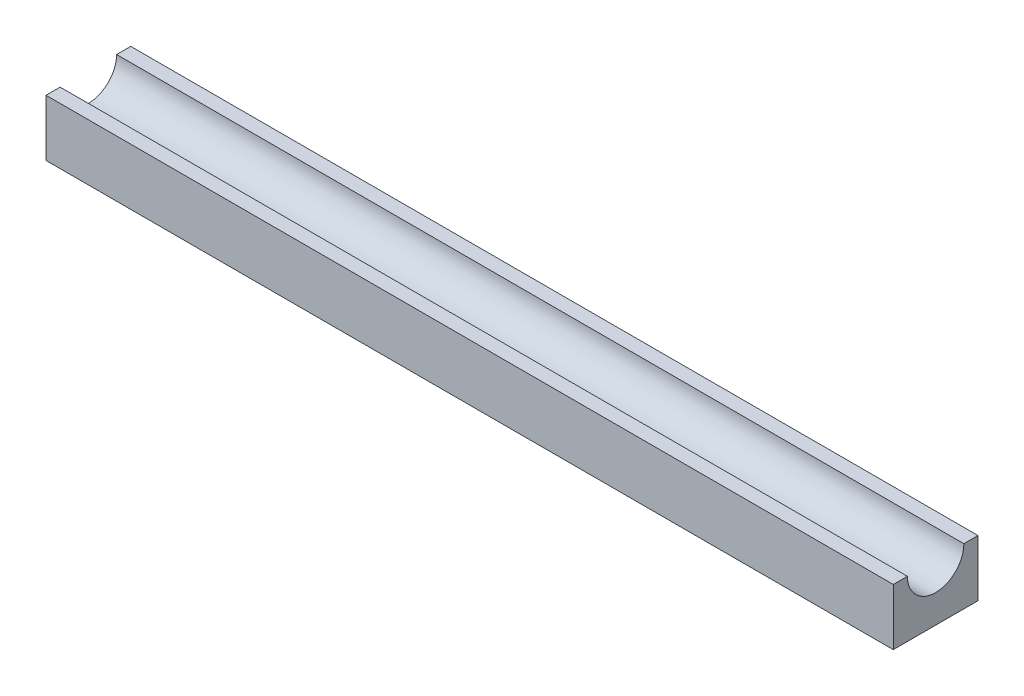
SolidWorks part; units mm, degrees
ref_plane "Front Plane" through (0, 0, 0) normal (0, 0, 1) x (1, 0, 0)
ref_plane "Top Plane" through (0, 0, 0) normal (0, 1, 0) x (1, 0, 0)
ref_plane "Right Plane" through (0, 0, 0) normal (1, 0, 0) x (0, 0, -1)
sketch "Sketch1" plane through (0, 0, 0) normal (1, 0, 0) x (0, 0, -1)
  line L1 (-7.5, 5) -> (7.5, 5)
  line L2 (-7.5, 5) -> (-7.5, -5)
  line L3 (-7.5, -5) -> (7.5, -5)
  line L4 (7.5, 5) -> (7.5, -5)
  line L5 (-7.5, 5) -> (7.5, -5) construction
  line L6 (-7.5, -5) -> (7.5, 5) construction
  circle A1 centre (0, 5) radius 5
  point P0 (0, 0)
  dimension "D3" = 10
  dimension "D1" = 10
  dimension "D2" = 15
extrude "Boss-Extrude1" add sketch "Sketch1" along normal blind 150
ref_plane "Plane1" through (15, 0, 0) normal (-1, 0, 0) x (0, 0, 1)
sketch "Sketch3" plane through (15, 0, 0) normal (-1, 0, 0) x (0, 0, 1)
  line L0 (7.5, -5) -> (-7.5, -5) construction
  line L1 (1.5, -5) -> (-1.5, -5)
  line L2 (1.5, -5) -> (1.5, -7)
  line L3 (1.5, -7) -> (-1.5, -7)
  line L4 (-1.5, -5) -> (-1.5, -7)
  line L5 (1.5, -5) -> (-1.5, -7) construction
  line L6 (1.5, -7) -> (-1.5, -5) construction
  arc A0 (-1.5, -7) -> (1.5, -7) centre (0, -7) ccw
  circle A1 centre (0, -7) radius 0.5
  point P0 (0, -6)
  point P7 (0, -5)
  point P8 (0, -5)
  dimension "D3" = 1
  dimension "D1" = 2
  dimension "D2" = 3
ref_plane "Plane2" through (82.5, 0, 0) normal (1, 0, 0) x (0, 0, -1)
ref_plane "Plane3" through (0, 0, 0) normal (0, 0, 1) x (1, 0, 0)
sketch "Sketch6" plane through (0, 0, 0) normal (0, 0, 1) x (1, 0, 0)
  line L0 (150, -5) -> (0, -5) construction
  line L1 (72.5, -5) -> (77.5, -5)
  line L2 (72.5, -5) -> (72.5, -8)
  line L3 (72.5, -8) -> (77.5, -8)
  line L4 (77.5, -5) -> (77.5, -8)
  line L5 (72.5, -5) -> (77.5, -8) construction
  line L6 (72.5, -8) -> (77.5, -5) construction
  line L7 (150, -5) -> (0, -5)
  line L8 (150, 5) -> (150, -5) construction
  circle A0 centre (75, -8) radius 2.5
  point P0 (75, -6.5)
  dimension "D1" = 5
  dimension "D2" = 75
  dimension "D3" = 3
extrude "Boss-Extrude6" add sketch "Sketch6" along normal mid plane 3 contours L3 A0 | L3 A0 | A0 L4 L1 L2
sketch "Sketch7" plane through (0, 0, 0) normal (0, 0, 1) x (1, 0, 0)
  arc A0 (72.5, -8) -> (77.5, -8) centre (75, -8) ccw construction
  arc A1 (72.5, -8) -> (77.5, -8) centre (75, -8) ccw
  circle A2 centre (75, -8) radius 0.5
  dimension "D1" = 1
ref_plane "Plane4" through (45, 0, 0) normal (-1, 0, 0) x (0, 0, 1)
mirror "Mirror1" about plane through (45, 0, 0) normal (-1, 0, 0) of "Boss-Extrude6"
extrude "Cut-Extrude1" cut sketch "Sketch7" against normal through all both and the other way through all contours A2
sketch "Sketch9" plane through (0, 0, 1.5) normal (0, 0, 1) x (1, 0, 0)
  circle A0 centre (15, -8) radius 0.5
  dimension "D1" = 1
extrude "Cut-Extrude2" cut sketch "Sketch9" against normal blind 10
